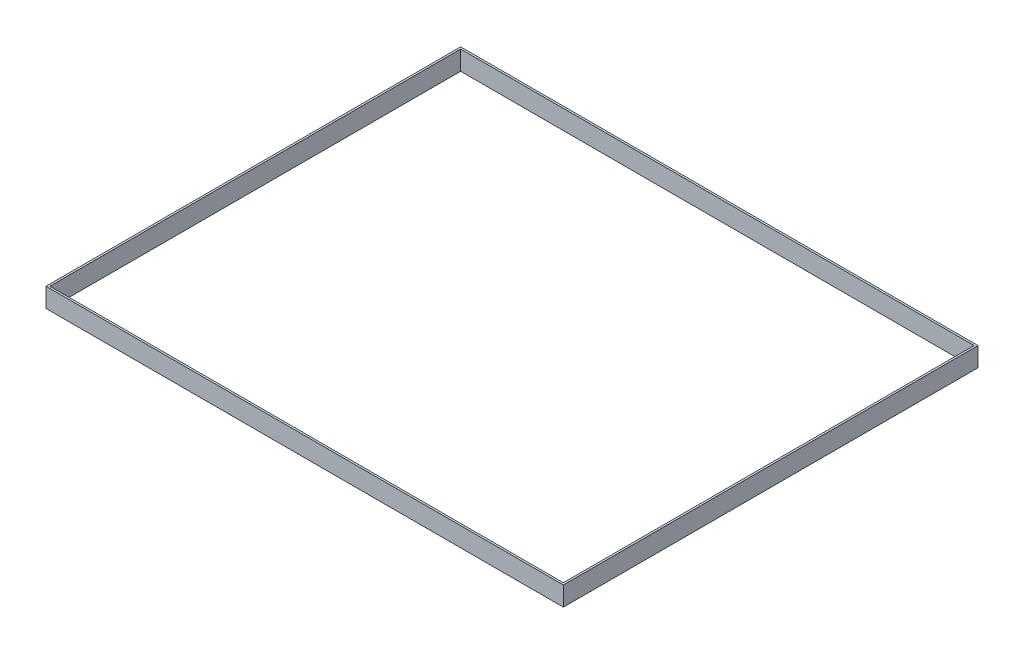
SolidWorks part; units mm, degrees
ref_plane "前视基准面" through (0, 0, 0) normal (0, 0, 1) x (1, 0, 0)
ref_plane "上视基准面" through (0, 0, 0) normal (0, 1, 0) x (1, 0, 0)
ref_plane "右视基准面" through (0, 0, 0) normal (1, 0, 0) x (0, 0, -1)
sketch "草图1" plane through (0, 0, 0) normal (0, 1, 0) x (1, 0, 0)
  line L1 (0, 0) -> (4000, 0)
  line L2 (0, 0) -> (0, 3200)
  line L3 (0, 3200) -> (4000, 3200)
  line L4 (4000, 0) -> (4000, 3200)
  line L5 (-15, -15) -> (4015, -15)
  line L6 (-15, -15) -> (-15, 3215)
  line L7 (-15, 3215) -> (4015, 3215)
  line L8 (4015, -15) -> (4015, 3215)
  dimension "D1" = 3200
  dimension "D2" = 4000
  dimension "D3" = 15
  dimension "D4" = 15
  dimension "D5" = 15
  dimension "D6" = 15
extrude "凸台-拉伸1" add sketch "草图1" along normal blind 150
